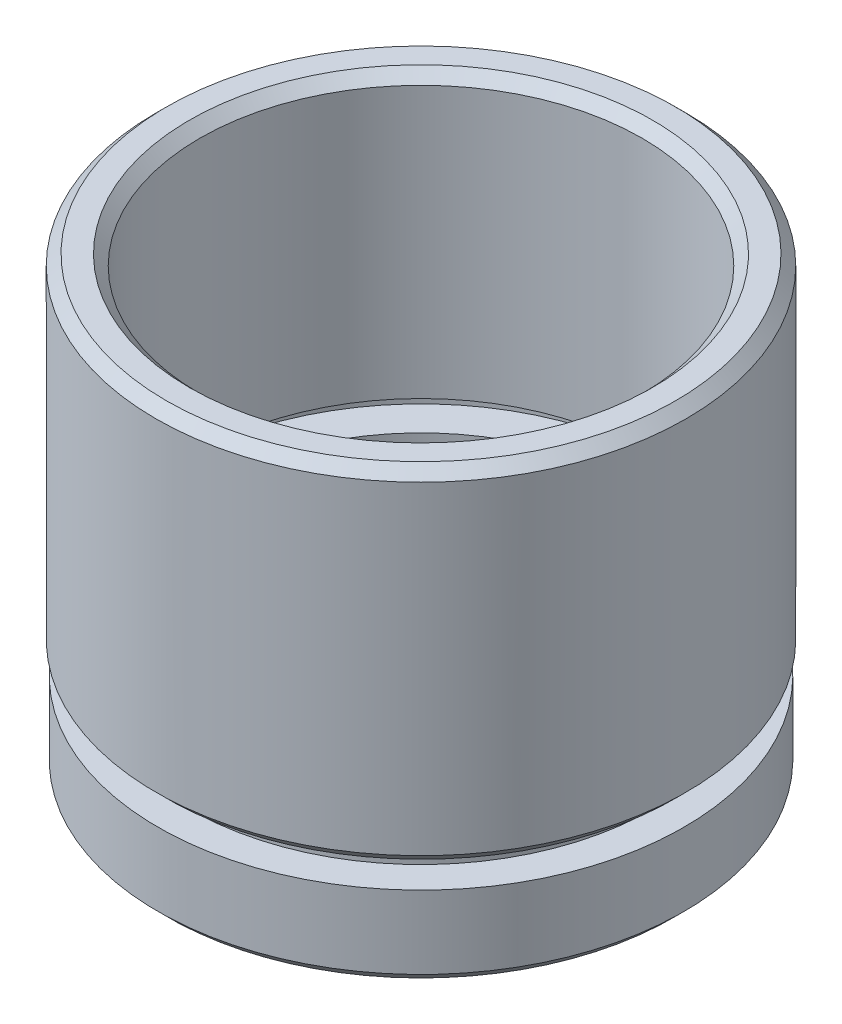
SolidWorks part; units mm, degrees
ref_plane "前视基准面" through (0, 0, 0) normal (0, 0, 1) x (1, 0, 0)
ref_plane "上视基准面" through (0, 0, 0) normal (0, 1, 0) x (1, 0, 0)
ref_plane "右视基准面" through (0, 0, 0) normal (1, 0, 0) x (0, 0, -1)
sketch "草图1" plane through (0, 0, 0) normal (0, 0, 1) x (1, 0, 0)
  line L0 (0, 0) -> (0, 21.8535) construction
  line L1 (9.25, 0) -> (12.6, 0)
  line L2 (12.6, 0) -> (12.6, 4)
  line L3 (12.6, 4) -> (11.1, 4)
  line L4 (11.1, 4) -> (11.1, 5)
  line L5 (11.1, 5) -> (12.7, 5)
  line L6 (12.7, 5) -> (12.7, 21.5)
  line L7 (12.7, 21.5) -> (10.6, 21.5)
  line L8 (10.6, 21.5) -> (10.6, 8)
  line L9 (10.6, 8) -> (11.7, 8)
  line L10 (11.7, 8) -> (11.7, 7)
  line L11 (11.7, 7) -> (10, 7)
  line L12 (10, 7) -> (10, 2)
  line L13 (10, 2) -> (9.25, 2)
  line L14 (9.25, 0) -> (9.25, 2)
  dimension "D1" = 21.5
  dimension "D2" = 12.7
  dimension "D3" = 10.6
  dimension "D4" = 10
  dimension "D5" = 1
  dimension "D6" = 5
  dimension "D7" = 9.25
  dimension "D8" = 12.6
  dimension "D9" = 1
  dimension "D10" = 5
  dimension "D11" = 2
  dimension "D12" = 11.7
  dimension "D13" = 11.1
revolve "旋转1" add sketch "草图1" angle 360 about L0
cosmetic thread "装饰螺纹线11" parameters "D2"=23.2
cosmetic thread "装饰螺纹线12" parameters "D2"=23.2
chamfer "倒角1" distance 0.5 angle 45 4 edges at (0, 21.5, -10.6) (0, 21.5, -12.7) (0, 5, -12.7) (0, 0, -12.6)
